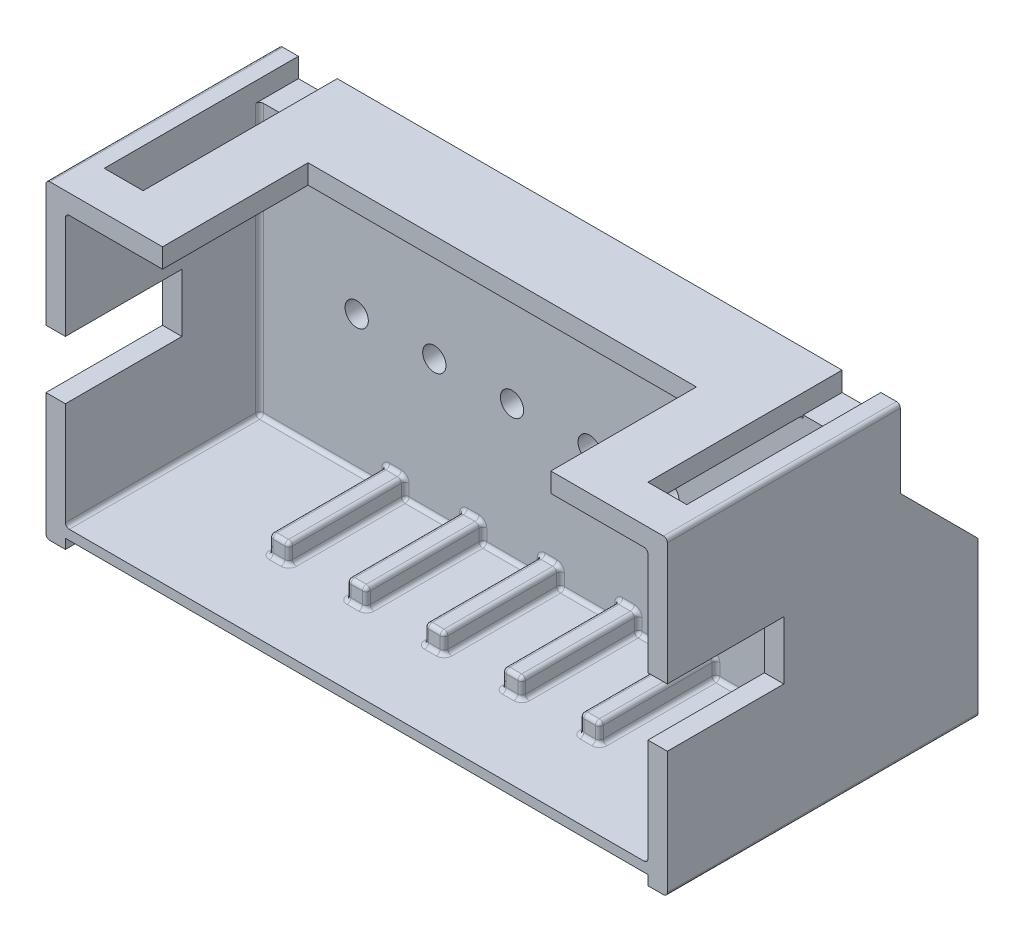
SolidWorks part; units mm, degrees
ref_plane "Ön Düzlem" through (0, 0, 0) normal (0, 0, 1) x (1, 0, 0)
ref_plane "Üst Düzlem" through (0, 0, 0) normal (0, 1, 0) x (1, 0, 0)
ref_plane "Sağ Düzlem" through (0, 0, 0) normal (1, 0, 0) x (0, 0, -1)
sketch "Sketch1" plane through (0, 0, 0) normal (0, 0, 1) x (1, 0, 0)
  line L1 (0, 0) -> (16, 0)
  line L2 (0, 0) -> (0, 8)
  line L3 (0, 8) -> (16, 8)
  line L4 (16, 0) -> (16, 8)
  circle A0 centre (3, 4) radius 0.3
  circle A1 centre (5, 4) radius 0.3
  circle A2 centre (7, 4) radius 0.3
  circle A3 centre (9, 4) radius 0.3
  circle A4 centre (11, 4) radius 0.3
  circle A5 centre (13, 4) radius 0.3
  dimension "D3" = 0.6
  dimension "D5" = 3
  dimension "D6" = 4
  dimension "D1" = 8
  dimension "D2" = 16
  dimension "D4" = 6
extrude "Boss-Extrude1" add sketch "Sketch1" along normal blind 8
sketch "Sketch2" plane through (0, 0, 8) normal (0, 0, 1) x (1, 0, 0)
  line L0 (0, 8) -> (0, 0) construction
  line L1 (0.5, 7.5) -> (15.5, 7.5)
  line L2 (0.5, 7.5) -> (0.5, 0.5)
  line L3 (0.5, 0.5) -> (15.5, 0.5)
  line L4 (15.5, 7.5) -> (15.5, 0.5)
  line L5 (16, 8) -> (0, 8) construction
  line L6 (16, 0) -> (16, 8) construction
  line L7 (0, 0) -> (16, 0) construction
  dimension "D1" = 0.5
  dimension "D2" = 0.5
  dimension "D3" = 0.5
  dimension "D4" = 0.5
extrude "Cut-Extrude1" cut sketch "Sketch2" against normal blind 5
sketch "Sketch4" plane through (0, 8, 0) normal (0, 1, 0) x (1, 0, 0)
  line L0 (16, 0) -> (0, 0) construction
  line L1 (0.5, 0) -> (15.5, 0)
  line L2 (0.5, 0) -> (0.5, -2)
  line L3 (0.5, -2) -> (15.5, -2)
  line L4 (15.5, 0) -> (15.5, -2)
  line L5 (0, -8) -> (0, 0) construction
  line L6 (16, -8) -> (16, 0) construction
  dimension "D1" = 2
  dimension "D2" = 0.5
  dimension "D3" = 0.5
extrude "Cut-Extrude2" cut sketch "Sketch4" against normal through all
sketch "Sketch5" plane through (16, 0, 0) normal (1, 0, 0) x (0, 0, -1)
  line L0 (-2, 8) -> (0, 8)
  line L1 (-8, 8) -> (0, 8) construction
  line L2 (0, 8) -> (0, 4)
  line L3 (0, 0) -> (0, 8) construction
  line L4 (0, 4) -> (-2, 6)
  line L5 (-2, 6) -> (-2, 8)
  dimension "D1" = 2
  dimension "D2" = 2
  dimension "D3" = 4
extrude "Cut-Extrude3" cut sketch "Sketch5" against normal through all
sketch "Sketch6" plane through (0, 8, 0) normal (0, 1, 0) x (1, 0, 0)
  line L0 (16, -8) -> (0, -8) construction
  line L1 (3, -8) -> (13, -8)
  line L2 (3, -8) -> (3, -4.2508)
  line L3 (3, -4.2508) -> (13, -4.2508)
  line L4 (13, -8) -> (13, -4.2508)
  line L5 (0, -8) -> (0, -2) construction
  dimension "D1" = 10
  dimension "D2" = 3
extrude "Cut-Extrude4" cut sketch "Sketch6" against normal up to next
sketch "Sketch7" plane through (0, 8, 0) normal (0, 1, 0) x (1, 0, 0)
  line L0 (0.5, -2) -> (0.5, -7)
  line L1 (0.5, -7) -> (1.5, -7)
  line L2 (1.5, -7) -> (1.5, -2)
  line L3 (0, -2) -> (16, -2) construction
  line L4 (1.5, -2) -> (0.5, -2)
  line L5 (8, -2) -> (8, -8) construction
  line L6 (0.5, -8) -> (15.5, -8) construction
  line L7 (0, -8) -> (0, -2) construction
  line L8 (14.5, -2) -> (15.5, -2)
  line L9 (14.5, -7) -> (14.5, -2)
  line L10 (15.5, -7) -> (14.5, -7)
  line L11 (15.5, -2) -> (15.5, -7)
  dimension "D1" = 0.5
  dimension "D2" = 1
  dimension "D3" = 5
extrude "Cut-Extrude5" cut sketch "Sketch7" against normal blind 0.5
sketch "Sketch8" plane through (0, 0.5, 0) normal (0, 1, 0) x (1, 0, 0)
  line L0 (3.75, -3) -> (3.75, -6)
  line L1 (0.5, -3) -> (15.5, -3) construction
  line L2 (3.75, -6) -> (4.25, -6)
  line L3 (4.25, -6) -> (4.25, -3)
  line L4 (4.25, -3) -> (3.75, -3)
  line L5 (0, -8) -> (0, 0) construction
  line L6 (5.75, -3) -> (5.75, -6)
  line L7 (5.75, -6) -> (6.25, -6)
  line L8 (6.25, -6) -> (6.25, -3)
  line L9 (6.25, -3) -> (5.75, -3)
  line L10 (7.75, -3) -> (7.75, -6)
  line L11 (7.75, -6) -> (8.25, -6)
  line L12 (8.25, -6) -> (8.25, -3)
  line L13 (8.25, -3) -> (7.75, -3)
  line L14 (9.75, -3) -> (9.75, -6)
  line L15 (9.75, -6) -> (10.25, -6)
  line L16 (10.25, -6) -> (10.25, -3)
  line L17 (10.25, -3) -> (9.75, -3)
  line L18 (11.75, -3) -> (11.75, -6)
  line L19 (11.75, -6) -> (12.25, -6)
  line L20 (12.25, -6) -> (12.25, -3)
  line L21 (12.25, -3) -> (11.75, -3)
  dimension "D1" = 0.5
  dimension "D2" = 3.75
  dimension "D4" = 3
  dimension "D3" = 5
extrude "Boss-Extrude2" add sketch "Sketch8" along normal blind 0.5
sketch "Sketch9" plane through (16, 0, 0) normal (1, 0, 0) x (0, 0, -1)
  line L0 (-8, 0) -> (-8, 8) construction
  line L1 (-8, 4.75) -> (-5, 4.75)
  line L2 (-8, 4.75) -> (-8, 3.25)
  line L3 (-8, 3.25) -> (-5, 3.25)
  line L4 (-5, 4.75) -> (-5, 3.25)
  line L8 (-8, 0) -> (0, 0) construction
  dimension "D1" = 3
  dimension "D2" = 1.5
  dimension "D3" = 3.25
extrude "Cut-Extrude6" cut sketch "Sketch9" against normal through all
sketch "Sketch10" plane through (0, 0, 8) normal (0, 0, 1) x (1, 0, 0)
  line L0 (15.5, 0.5) -> (15.5, 3.25) construction
  line L1 (0.5, 0) -> (15.5, 0)
  line L2 (0.5, 0) -> (0.5, 0.25)
  line L3 (0.5, 0.25) -> (15.5, 0.25)
  line L4 (15.5, 0) -> (15.5, 0.25)
  dimension "D1" = 0
  dimension "D2" = 0.25
extrude "Cut-Extrude7" cut sketch "Sketch10" against normal through all
fillet "Fillet1" radius 0.1 76 edges at (4.25, 0.75, 3) (3.75, 0.75, 3) (3.75, 0.5, 4.5) (4.25, 0.5, 4.5) (5.75, 0.5, 4.5) (6.25, 0.5, 4.5) (11.75, 0.5, 4.5) (12.25, 0.5, 4.5) (9.75, 0.5, 4.5) (10.25, 0.5, 4.5) (7.75, 0.5, 4.5) (8.25, 0.5, 4.5) (6.25, 0.75, 3) (5.75, 0.75, 3) (8.25, 0.75, 3) (7.75, 0.75, 3) (10.25, 0.75, 3) (9.75, 0.75, 3) (12.25, 0.75, 3) (11.75, 0.75, 3) (4.25, 1, 4.5) (3.75, 1, 4.5) (4, 1, 3) (3.75, 0.75, 6) (4, 1, 6) (4.25, 0.75, 6) (4, 0.5, 6) (5.75, 0.75, 6) (6.25, 0.75, 6) (6, 0.5, 6) (11.75, 0.75, 6) (12.25, 0.75, 6) (12, 0.5, 6) (9.75, 0.75, 6) (10.25, 0.75, 6) (10, 0.5, 6) (7.75, 0.75, 6) (8.25, 0.75, 6) (8, 0.5, 6) (6.25, 1, 4.5) (6, 1, 6) (5.75, 1, 4.5) (6, 1, 3) (8.25, 1, 4.5) (8, 1, 6) (7.75, 1, 4.5) (8, 1, 3) (10.25, 1, 4.5) (10, 1, 6) (9.75, 1, 4.5) (10, 1, 3) (12.25, 1, 4.5) (12, 1, 6) (11.75, 1, 4.5) (12, 1, 3) (11, 0.5, 3) (9, 0.5, 3) (7, 0.5, 3) (13.875, 0.5, 3) (15.5, 4, 3) (8, 7.5, 3) (0.5, 7.5, 7.5) (0.5, 4, 3) (5, 0.5, 3) (2.125, 0.5, 3) (0.5, 0.5, 5.5) (0, 0, 4) (16, 0, 4) (16, 8, 5) (0, 8, 5) (15.5, 7.5, 7.5) (15.75, 4, 0) (15.75, 6, 2) (0.25, 6, 2) (0.25, 4, 0) (15.5, 0.5, 5.5)
